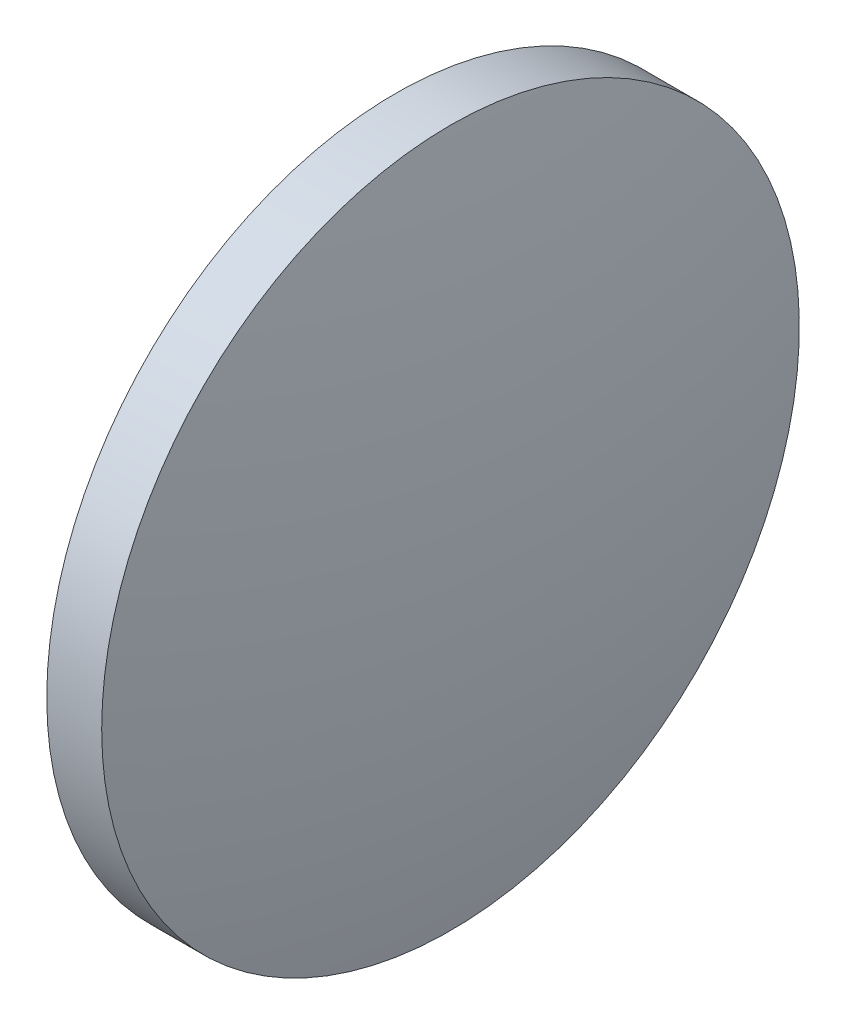
SolidWorks part; units mm, degrees
ref_plane "前视基准面" through (0, 0, 0) normal (0, 0, 1) x (1, 0, 0)
ref_plane "上视基准面" through (0, 0, 0) normal (0, 1, 0) x (1, 0, 0)
ref_plane "右视基准面" through (0, 0, 0) normal (1, 0, 0) x (0, 0, -1)
sketch "草图1" plane through (0, 0, 0) normal (0, 0, 1) x (1, 0, 0)
  line L0 (444.1034, 96.7243) -> (462.8994, 96.7243) construction
  line L1 (449.8416, 96.7243) -> (449.8416, 109.4243)
  line L2 (449.8416, 109.4243) -> (451.8416, 109.4243)
  line L3 (453.1416, 96.7243) -> (449.8416, 96.7243)
  arc A0 (453.1416, 96.7243) -> (451.8416, 109.4243) centre (390.457, 96.7243) ccw
revolve "旋转1" add sketch "草图1" angle 360 about L0
